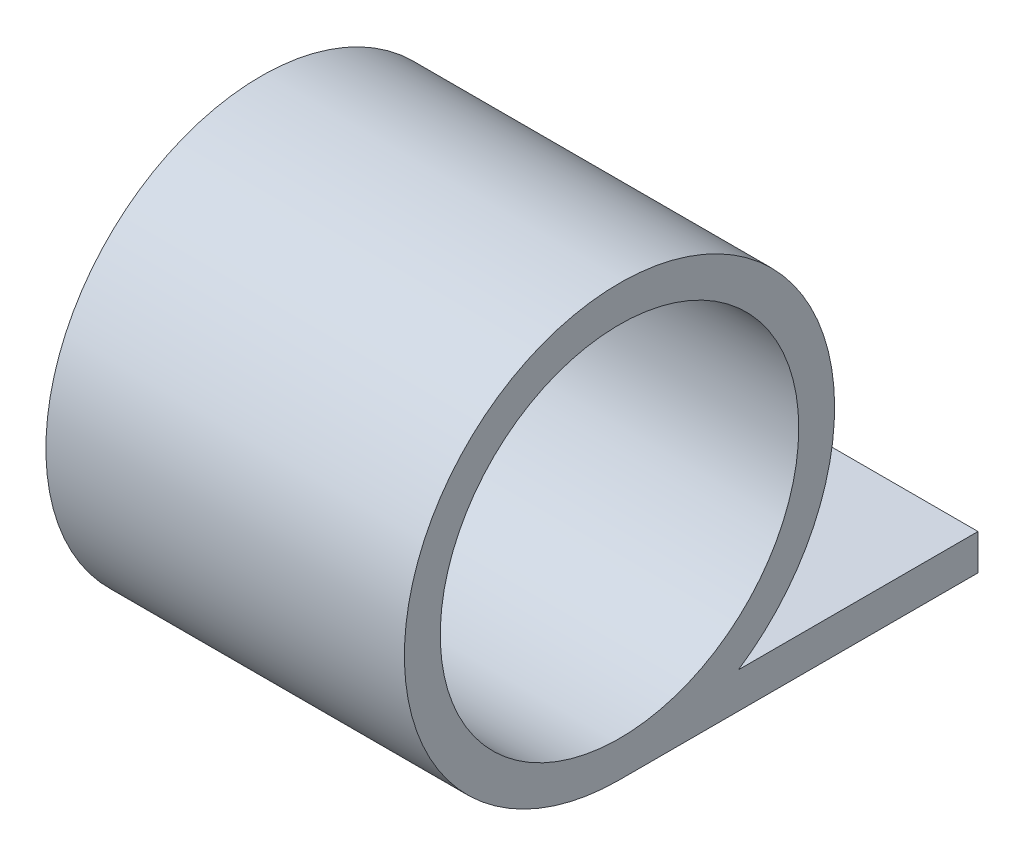
SolidWorks part; units mm, degrees
ref_plane "Front Plane" through (0, 0, 0) normal (0, 0, 1) x (1, 0, 0)
ref_plane "Top Plane" through (0, 0, 0) normal (0, 1, 0) x (1, 0, 0)
ref_plane "Right Plane" through (0, 0, 0) normal (1, 0, 0) x (0, 0, -1)
sketch "Sketch1" plane through (0, 0, 0) normal (1, 0, 0) x (0, 0, -1)
  line L0 (10, -5) -> (3.3166, -5)
  line L1 (10, -6) -> (0, -6)
  line L5 (10, -5) -> (10, -6)
  arc A0 (3.3166, -5) -> (0, -6) centre (0, 0) ccw
  circle A1 centre (0, 0) radius 5
  point P0 (0, 0)
extrude "Boss-Extrude1" add sketch "Sketch1" along normal blind 10
